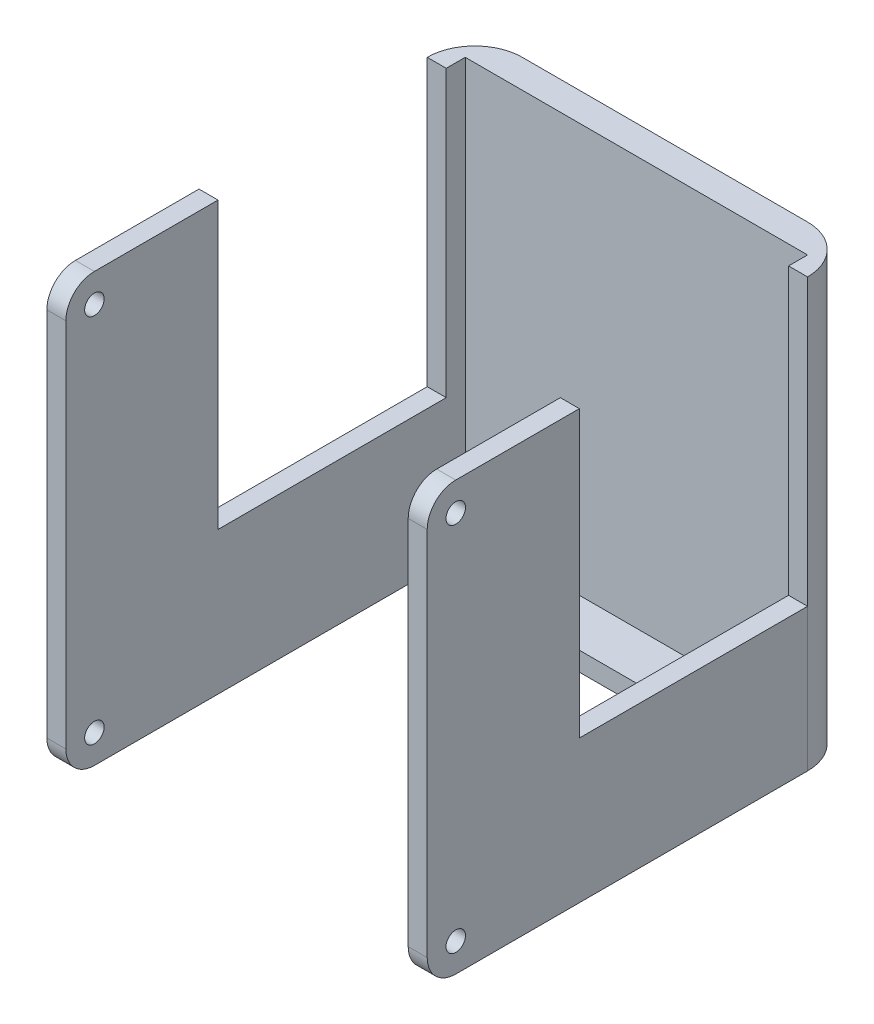
SolidWorks part; units mm, degrees
ref_plane "前基準面" through (0, 0, 0) normal (0, 0, 1) x (1, 0, 0)
ref_plane "上基準面" through (0, 0, 0) normal (0, 1, 0) x (1, 0, 0)
ref_plane "右基準面" through (0, 0, 0) normal (1, 0, 0) x (0, 0, -1)
sketch "草圖1" plane through (0, 0, 0) normal (0, 0, 1) x (1, 0, 0)
  line L1 (-14.5455, 16.9091) -> (25.4545, 16.9091)
  line L2 (-14.5455, 16.9091) -> (-14.5455, -28.0909)
  line L3 (-14.5455, -28.0909) -> (25.4545, -28.0909)
  line L4 (25.4545, 16.9091) -> (25.4545, -28.0909)
  dimension "D1" = 40
  dimension "D2" = 45
extrude "填料-伸長1" add sketch "草圖1" along normal blind 40 and the other way blind 5 contours L4 L3 L2 L1
sketch "草圖2" plane through (0, 16.9091, 0) normal (0, 1, 0) x (1, 0, 0)
  line L0 (5.4545, 5) -> (5.4545, -40.6532) construction
  line L1 (-14.5455, 5) -> (25.4545, 5) construction
  line L2 (-14.5455, -40) -> (25.4545, -40) construction
  line L3 (-12.5455, -3) -> (23.4545, -3)
  line L4 (-12.5455, -3) -> (-12.5455, -40)
  line L5 (-12.5455, -40) -> (23.4545, -40)
  line L6 (23.4545, -3) -> (23.4545, -40)
  line L7 (-14.5455, -40) -> (-14.5455, 5) construction
  line L8 (25.4545, -40) -> (25.4545, 5) construction
  dimension "D1" = 2
  dimension "D2" = 2
  dimension "D3" = 37
extrude "除料-伸長1" cut sketch "草圖2" against normal blind 50
sketch "草圖3" plane through (-14.5455, 0, 0) normal (-1, 0, 0) x (0, 0, 1)
  line L1 (40, -28.0909) -> (-5, -28.0909) construction
  line L2 (40, 16.9091) -> (40, -28.0909) construction
  line L3 (40, 16.9091) -> (-5, 16.9091) construction
  circle A1 centre (37, -25.0909) radius 1.025
  circle A2 centre (37, 13.9091) radius 1.025
  dimension "D5" = 3
  dimension "D6" = 2.05
  dimension "D1" = 2.05
  dimension "D2" = 3
  dimension "D3" = 3
  dimension "D4" = 3
extrude "除料-伸長2" cut sketch "草圖3" against normal blind 2
sketch "草圖4" plane through (25.4545, 0, 0) normal (1, 0, 0) x (0, 0, -1)
  line L0 (-40, 16.9091) -> (-40, -28.0909) construction
  line L1 (-40, -28.0909) -> (5, -28.0909) construction
  line L2 (-40, 16.9091) -> (5, 16.9091) construction
  circle A0 centre (-37, 13.9091) radius 1.025
  circle A1 centre (-37, -25.0909) radius 1.025
  dimension "D1" = 2.05
  dimension "D2" = 2.05
  dimension "D3" = 3
  dimension "D4" = 3
  dimension "D5" = 3
  dimension "D6" = 3
extrude "除料-伸長3" cut sketch "草圖4" against normal blind 2
sketch "草圖5" plane through (0, 16.9091, 0) normal (0, 1, 0) x (1, 0, 0)
  line L1 (-12.5455, -3) -> (23.4545, -3)
  line L2 (-12.5455, -3) -> (-12.5455, 2)
  line L3 (-12.5455, 2) -> (23.4545, 2)
  line L4 (23.4545, -3) -> (23.4545, 2)
  dimension "D1" = 36
  dimension "D2" = 5
extrude "除料-伸長4" cut sketch "草圖5" against normal blind 43
fillet "圓角6" radius 5 1 edges at (-14.5455, -5.5909, -5)
fillet "圓角7" radius 5 1 edges at (25.4545, -5.5909, -5)
fillet "圓角12" radius 3 1 edges at (-13.5455, -28.0909, 40)
fillet "圓角13" radius 3 1 edges at (24.4545, -28.0909, 40)
fillet "圓角14" radius 3 1 edges at (-13.5455, 16.9091, 40)
fillet "圓角15" radius 3 1 edges at (24.4545, 16.9091, 40)
ref_plane "平面1" through (-14.5455, 0, 0) normal (-1, 0, 0) x (0, 0, 1)
sketch "草圖6" plane through (-14.5455, 0, 0) normal (-1, 0, 0) x (0, 0, 1)
  line L0 (0, 16.9091) -> (37, 16.9091) construction
  line L1 (0, -13.0909) -> (24, -13.0909)
  line L2 (0, -13.0909) -> (0, 16.9091)
  line L3 (0, 16.9091) -> (24, 16.9091)
  line L4 (24, -13.0909) -> (24, 16.9091)
  line L5 (0, 16.9091) -> (0, -28.0909) construction
  line L6 (0, -28.0909) -> (37, -28.0909) construction
  dimension "D1" = 0
  dimension "D2" = 24
  dimension "D3" = 15
extrude "除料-伸長5" cut sketch "草圖6" against normal blind 44
